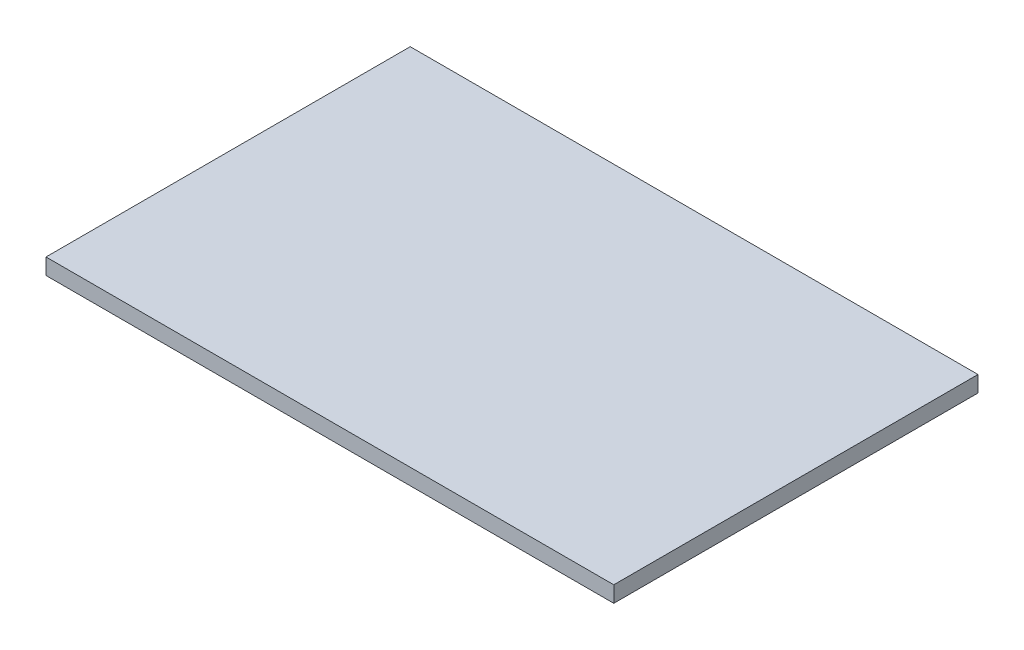
SolidWorks part; units mm, degrees
ref_plane "Front Plane" through (0, 0, 0) normal (0, 0, 1) x (1, 0, 0)
ref_plane "Top Plane" through (0, 0, 0) normal (0, 1, 0) x (1, 0, 0)
ref_plane "Right Plane" through (0, 0, 0) normal (1, 0, 0) x (0, 0, -1)
sketch "Sketch2" plane through (0, 0, 0) normal (0, 1, 0) x (1, 0, 0)
  line L1 (2778.4235, 891.3043) -> (2913.0435, 891.3043)
  line L2 (2778.4235, 891.3043) -> (2778.4235, 804.9443)
  line L3 (2778.4235, 804.9443) -> (2913.0435, 804.9443)
  line L4 (2913.0435, 891.3043) -> (2913.0435, 804.9443)
  dimension "D1" = 134.62
  dimension "D2" = 86.36
extrude "Boss-Extrude1" add sketch "Sketch2" along normal blind 3.81
